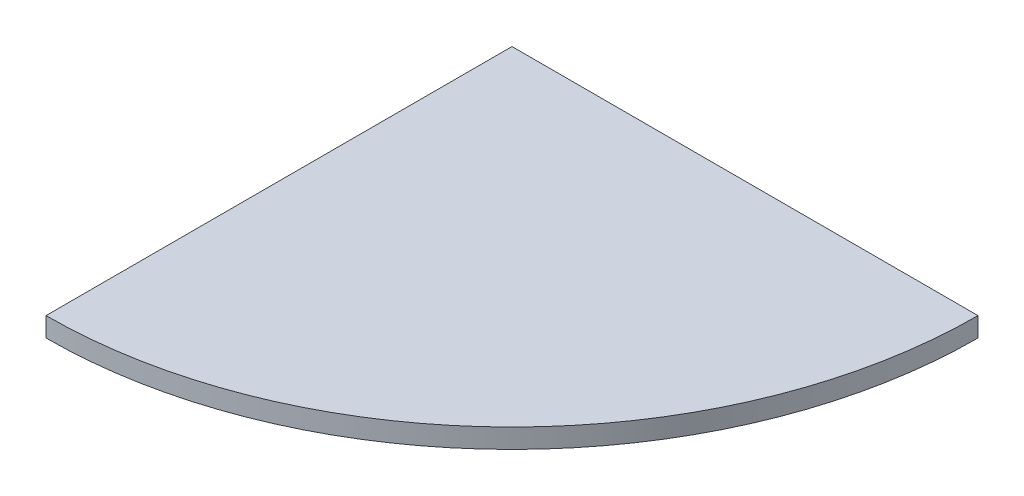
SolidWorks part; units mm, degrees
ref_plane "Front Plane" through (0, 0, 0) normal (0, 0, 1) x (1, 0, 0)
ref_plane "Top Plane" through (0, 0, 0) normal (0, 1, 0) x (1, 0, 0)
ref_plane "Right Plane" through (0, 0, 0) normal (1, 0, 0) x (0, 0, -1)
sketch "Sketch1" plane through (0, 0, 0) normal (0, 1, 0) x (1, 0, 0)
  line L0 (0, 0) -> (0, -432)
  line L1 (0, 0) -> (432, 0)
  arc A0 (432, 0) -> (0, -432) centre (0, 0) cw
  dimension "D1" = 432
extrude "Boss-Extrude1" add sketch "Sketch1" along normal blind 18
